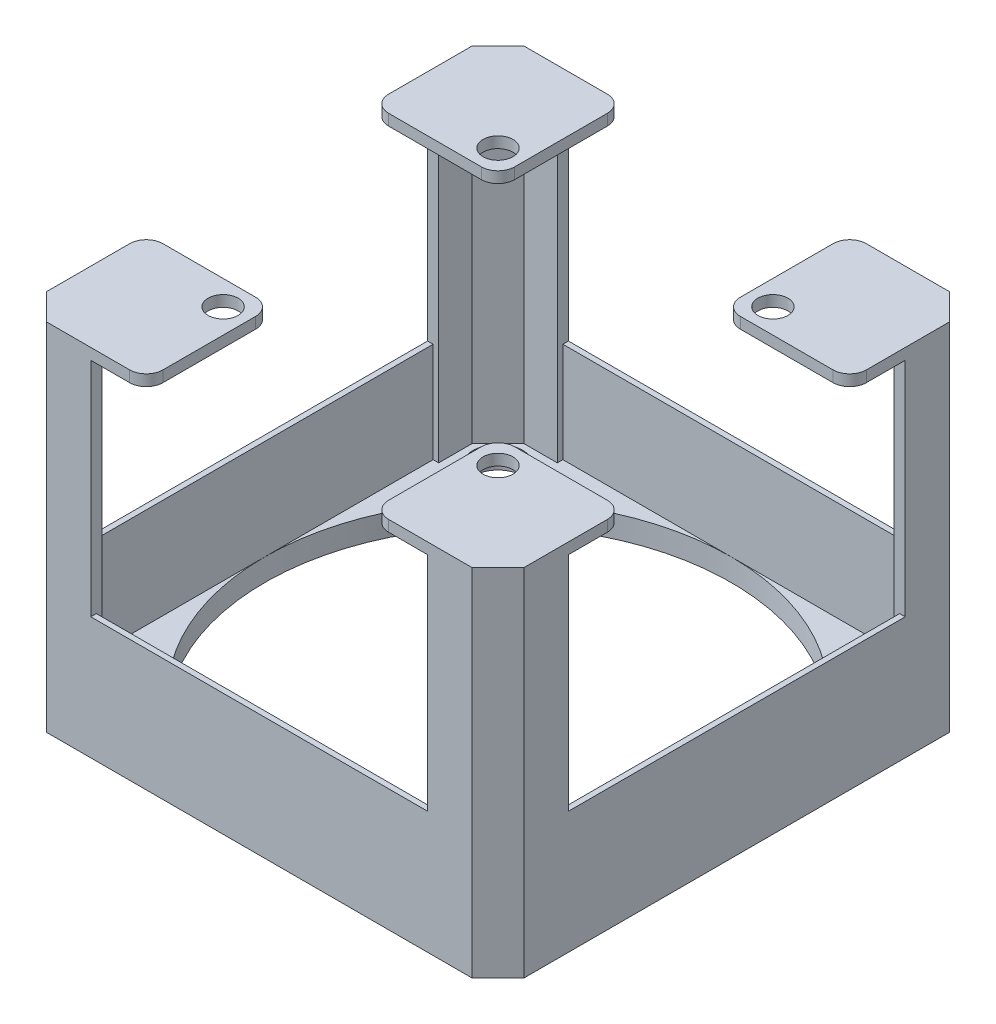
SolidWorks part; units mm, degrees
material "Wrought Stainless Steel"
ref_plane "Front Plane" through (0, 0, 0) normal (0, 0, 1) x (1, 0, 0)
ref_plane "Top Plane" through (0, 0, 0) normal (0, 1, 0) x (1, 0, 0)
ref_plane "Right Plane" through (0, 0, 0) normal (1, 0, 0) x (0, 0, -1)
sketch "Sketch1" plane through (0, 0, 0) normal (0, 1, 0) x (1, 0, 0)
  line L1 (0, 0) -> (38.3244, 0)
  line L2 (38.3244, 0) -> (40.6622, 2.3378)
  line L3 (40.6622, 2.3378) -> (40.6622, 40.6622)
  line L4 (40.6622, 40.6622) -> (38.3244, 43)
  line L5 (38.3244, 43) -> (0, 43)
  line L6 (0, 43) -> (-2.3378, 40.6622)
  line L7 (-2.3378, 40.6622) -> (-2.3378, 2.3378)
  line L8 (-2.3378, 2.3378) -> (0, 0)
  circle A0 centre (19.1622, 21.5) radius 21
extrude "Boss-Extrude1" add sketch "Sketch1" along normal blind 2 contours A0 | L8 L1 L2 L3 L4 L5 L6 L7
sketch "Sketch3" plane through (0, 2, 0) normal (0, 1, 0) x (1, 0, 0)
  line L9 (0, 0) -> (38.3244, 0) construction
  line L10 (0, 0) -> (4, 0)
  line L11 (4, 0) -> (4, 1)
  line L12 (0, 0) -> (-2.3378, 2.3378)
  line L13 (-2.3378, 2.3378) -> (-2.3378, 6.3378)
  line L14 (38.3244, 43) -> (0, 43) construction
  line L15 (-2.3378, 36.6622) -> (-1.3378, 36.6622)
  line L16 (-1.3378, 36.6622) -> (-1.3378, 39.6622)
  line L17 (-1.3378, 39.6622) -> (1, 42)
  line L18 (1, 42) -> (4, 42)
  line L19 (40.6622, 2.3378) -> (40.6622, 40.6622) construction
  line L23 (37.3244, 42) -> (34.3244, 42)
  line L24 (38.3244, 0) -> (34.3244, 0)
  line L25 (34.3244, 0) -> (34.3244, 1)
  line L27 (40.6622, 36.6622) -> (39.6622, 36.6622)
  line L28 (39.6622, 36.6622) -> (39.6622, 39.6622)
  line L29 (4, 1) -> (1, 1)
  line L30 (-2.3378, 40.6622) -> (-2.3378, 2.3378) construction
  line L31 (-2.3378, 6.3378) -> (-1.3378, 6.3378)
  line L32 (-1.3378, 6.3378) -> (-1.3378, 3.3378)
  line L33 (-1.3378, 3.3378) -> (1, 1)
  line L34 (4, 42) -> (4, 43)
  line L35 (4, 43) -> (0, 43)
  line L36 (0, 43) -> (-2.3378, 40.6622)
  line L37 (-2.3378, 40.6622) -> (-2.3378, 36.6622)
  line L38 (34.3244, 42) -> (34.3244, 43)
  line L39 (34.3244, 43) -> (38.3244, 43)
  line L40 (38.3244, 43) -> (40.6622, 40.6622)
  line L41 (40.6622, 40.6622) -> (40.6622, 36.6622)
  line L42 (39.6622, 39.6622) -> (37.3244, 42)
  line L43 (34.3244, 1) -> (37.3244, 1)
  line L44 (37.3244, 1) -> (39.6622, 3.3378)
  line L45 (39.6622, 3.3378) -> (39.6622, 6.3378)
  line L46 (39.6622, 6.3378) -> (40.6622, 6.3378)
  line L47 (40.6622, 6.3378) -> (40.6622, 2.3378)
  line L48 (40.6622, 2.3378) -> (38.3244, 0)
  point P3 (19.1622, 0.5)
  point P4 (34.3244, 0)
  point P6 (40.1622, 21.5)
  point P7 (40.6622, 36.6622)
  point P8 (-2.3378, 40.6622)
  point P9 (19.1622, 42.5)
  point P10 (-2.3378, 36.6622)
  point P11 (0, 43)
  point P12 (-1.8378, 21.5)
  point P13 (-2.3378, 6.3378)
  point P14 (4, 0)
  point P21 (4, 43)
  point P24 (-2.3378, 2.3378)
  point P30 (38.3244, 0)
  line M3 (-2.3378, 40.6622) -> (-2.3378, 2.3378)
  line M4 (-2.3378, 2.3378) -> (0, 0)
  line M5 (0, 0) -> (38.3244, 0)
  line M6 (38.3244, 0) -> (40.6622, 2.3378)
  line M7 (40.6622, 2.3378) -> (40.6622, 40.6622)
  line M9 (38.3244, 43) -> (0, 43)
  line M10 (0, 43) -> (-2.3378, 40.6622)
extrude "Boss-Extrude6" add sketch "Sketch3" along normal blind 30 contours L46 L45 L44 L43 L25 M5 M6 M7 | L33 L32 L31 L11 L29 M3 M4 M5 | L18 L34 L15 L16 L17 M9 M10 M3 | L42 L23 L38 L39 L40 L41 L27 L28
sketch "Sketch13" plane through (0, 2, 0) normal (0, 1, 0) x (1, 0, 0)
  line L0 (4, 0.5) -> (34.3244, 0.5)
  line L1 (4, 0) -> (4, 1) construction
  line L2 (34.3244, 0) -> (34.3244, 1) construction
  line L3 (40.1622, 6.3378) -> (40.1622, 36.6622)
  line L4 (39.6622, 6.3378) -> (40.6622, 6.3378) construction
  line L5 (40.6622, 36.6622) -> (39.6622, 36.6622) construction
  line L6 (4, 42.5) -> (34.3244, 42.5)
  line L7 (4, 42) -> (4, 43) construction
  line L8 (34.3244, 42) -> (34.3244, 43) construction
  line L9 (-1.8378, 36.6622) -> (-1.8378, 6.3378)
  line L10 (-2.3378, 36.6622) -> (-1.3378, 36.6622) construction
  line L11 (-2.3378, 6.3378) -> (-1.3378, 6.3378) construction
  line L12 (-2.3378, 36.6622) -> (-2.3378, 6.3378)
  line L13 (4, 43) -> (34.3244, 43)
  line L14 (34.3244, 43) -> (4, 43)
  line L15 (4, 0) -> (34.3244, 0)
  line L16 (4, 0) -> (34.3244, 0) construction
  line L17 (40.6622, 36.6622) -> (40.6622, 6.3378)
  line M1 (40.6622, 36.6622) -> (39.6622, 36.6622)
  line M5 (34.3244, 42) -> (34.3244, 43)
  line M6 (34.3244, 43) -> (4, 43)
  line M7 (4, 43) -> (4, 42)
  line M11 (-1.3378, 36.6622) -> (-2.3378, 36.6622)
  line M12 (-2.3378, 36.6622) -> (-2.3378, 6.3378)
  line M13 (-2.3378, 6.3378) -> (-1.3378, 6.3378)
  line M17 (4, 1) -> (4, 0)
  line M18 (4, 0) -> (34.3244, 0)
  line M19 (34.3244, 0) -> (34.3244, 1)
  line M23 (39.6622, 6.3378) -> (40.6622, 6.3378)
  line M24 (40.6622, 6.3378) -> (40.6622, 36.6622)
extrude "Boss-Extrude7" add sketch "Sketch13" along normal blind 9 contours L0 M17 M18 M19 | L9 M11 M12 M13 | L3 M23 M24 M1 | L6 M7 M5 M6
sketch "Sketch15" plane through (0, 32, 0) normal (0, 1, 0) x (1, 0, 0)
  line L0 (19.1622, 21.5) -> (31.5366, 21.5)
  line L1 (31.5366, 21.5) -> (31.5366, 33.8744)
  line L2 (19.1622, 21.5) -> (19.1622, 9.1256)
  line L3 (19.1622, 9.1256) -> (6.7878, 9.1256)
  line L32 (4, 0) -> (7.5, 0)
  line L34 (-2.3378, 6.3378) -> (-2.3378, 9.8378)
  line L38 (4, 0) -> (0, 0)
  line L39 (0, 0) -> (-2.3378, 2.3378)
  line L40 (-2.3378, 2.3378) -> (-2.3378, 6.3378)
  line L41 (-0.8378, 11.3378) -> (7.5, 11.3378)
  line L42 (9, 9.8378) -> (9, 1.5)
  line L44 (39.1622, 11.3378) -> (30.8244, 11.3378)
  line L45 (40.6622, 6.3378) -> (40.6622, 9.8378)
  line L46 (40.6622, 2.3378) -> (40.6622, 6.3378)
  line L47 (38.3244, 0) -> (40.6622, 2.3378)
  line L48 (34.3244, 0) -> (38.3244, 0)
  line L49 (34.3244, 0) -> (30.8244, 0)
  line L50 (29.3244, 9.8378) -> (29.3244, 1.5)
  line L51 (-0.8378, 31.6622) -> (7.5, 31.6622)
  line L52 (-2.3378, 36.6622) -> (-2.3378, 33.1622)
  line L53 (-2.3378, 40.6622) -> (-2.3378, 36.6622)
  line L54 (0, 43) -> (-2.3378, 40.6622)
  line L55 (4, 43) -> (0, 43)
  line L56 (4, 43) -> (7.5, 43)
  line L57 (9, 33.1622) -> (9, 41.5)
  line L58 (40.6622, 36.6622) -> (40.6622, 33.1622)
  line L59 (40.6622, 40.6622) -> (40.6622, 36.6622)
  line L60 (38.3244, 43) -> (40.6622, 40.6622)
  line L61 (34.3244, 43) -> (38.3244, 43)
  line L62 (34.3244, 43) -> (30.8244, 43)
  line L63 (29.3244, 33.1622) -> (29.3244, 41.5)
  line L64 (39.1622, 31.6622) -> (30.8244, 31.6622)
  circle A0 centre (31.5366, 33.8744) radius 1.35
  circle A1 centre (6.7878, 9.1256) radius 1.35
  circle A2 centre (6.7878, 33.8744) radius 1.35
  circle A3 centre (31.5366, 9.1256) radius 1.35
  arc A11 (-2.3378, 9.8378) -> (-0.8378, 11.3378) centre (-0.8378, 9.8378) cw
  arc A12 (7.5, 0) -> (9, 1.5) centre (7.5, 1.5) ccw
  arc A13 (7.5, 11.3378) -> (9, 9.8378) centre (7.5, 9.8378) cw
  arc A14 (40.6622, 9.8378) -> (39.1622, 11.3378) centre (39.1622, 9.8378) ccw
  arc A15 (30.8244, 0) -> (29.3244, 1.5) centre (30.8244, 1.5) cw
  arc A16 (30.8244, 11.3378) -> (29.3244, 9.8378) centre (30.8244, 9.8378) ccw
  arc A17 (-2.3378, 33.1622) -> (-0.8378, 31.6622) centre (-0.8378, 33.1622) ccw
  arc A18 (7.5, 43) -> (9, 41.5) centre (7.5, 41.5) cw
  arc A19 (7.5, 31.6622) -> (9, 33.1622) centre (7.5, 33.1622) ccw
  arc A20 (40.6622, 33.1622) -> (39.1622, 31.6622) centre (39.1622, 33.1622) cw
  arc A21 (30.8244, 43) -> (29.3244, 41.5) centre (30.8244, 41.5) ccw
  arc A22 (30.8244, 31.6622) -> (29.3244, 33.1622) centre (30.8244, 33.1622) cw
  dimension "D1" = 1.5
extrude "Boss-Extrude9" add sketch "Sketch15" against normal blind 1
sketch "Sketch16" plane through (0, 2, 0) normal (0, 1, 0) x (1, 0, 0)
  line L0 (19.1622, 21.5) -> (36.8399, 39.1777)
  line L1 (19.1622, 21.5) -> (36.8399, 3.8223)
  line L2 (19.1622, 21.5) -> (1.4845, 39.1777)
  line L3 (19.1622, 21.5) -> (1.4845, 3.8223)
  circle A0 centre (19.1622, 21.5) radius 25
  circle A1 centre (36.8399, 39.1777) radius 2.25
  circle A2 centre (36.8399, 3.8223) radius 2.25
  circle A3 centre (1.4845, 3.8223) radius 2.25
  circle A4 centre (1.4845, 39.1777) radius 2.25
extrude "Cut-Extrude1" cut sketch "Sketch16" against normal through all contours A4 | A1 | A2 | A3
